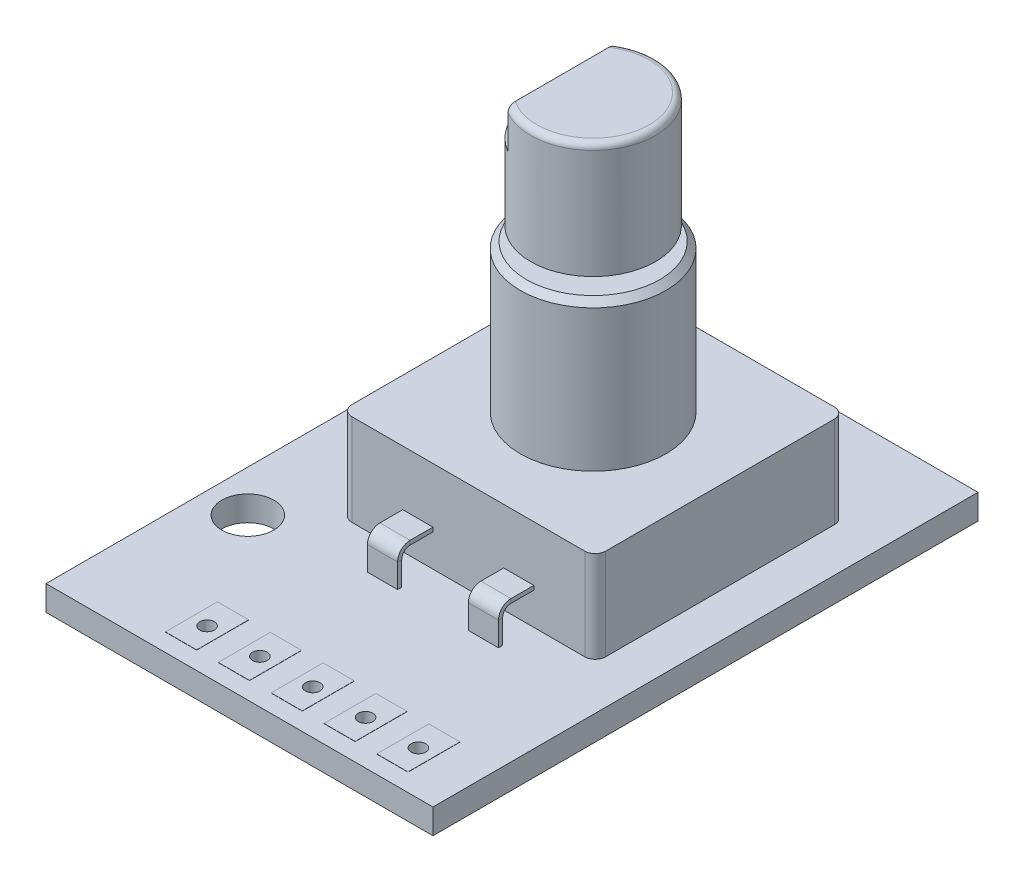
SolidWorks part; units mm, degrees
ref_plane "Front Plane" through (0, 0, 0) normal (0, 0, 1) x (1, 0, 0)
ref_plane "Top Plane" through (0, 0, 0) normal (0, 1, 0) x (1, 0, 0)
ref_plane "Right Plane" through (0, 0, 0) normal (1, 0, 0) x (0, 0, -1)
sketch "Sketch1" plane through (0, 0, 0) normal (0, 1, 0) x (1, 0, 0)
  line L0 (-7.3, 8.3) -> (-7.3, -5.4) construction
  line L1 (-9.3, 13.1) -> (9.3, 13.1)
  line L2 (-9.3, 13.1) -> (-9.3, -13.1)
  line L3 (-9.3, -13.1) -> (9.3, -13.1)
  line L4 (9.3, 13.1) -> (9.3, -13.1)
  line L5 (-9.3, 13.1) -> (9.3, -13.1) construction
  line L6 (-9.3, -13.1) -> (9.3, 13.1) construction
  circle A0 centre (-7.3, 8.3) radius 1.25
  circle A1 centre (-7.3, -5.4) radius 1.25
  point P0 (0, 0)
  dimension "D3" = 2.5
  dimension "D1" = 18.6
  dimension "D2" = 26.2
  dimension "D4" = 13.7
  dimension "D5" = 4.8
  dimension "D6" = 2
extrude "Boss-Extrude1" add sketch "Sketch1" along normal blind 1.2
sketch "Sketch3" plane through (0, 1.2, 0) normal (0, 1, 0) x (1, 0, 0)
  line L0 (9.3, -13.1) -> (9.3, 13.1) construction
  line L1 (-5, -3.2) -> (7.2, -3.2)
  line L2 (-5, -3.2) -> (-5, 8.8)
  line L3 (-5, 8.8) -> (7.2, 8.8)
  line L4 (7.2, -3.2) -> (7.2, 8.8)
  line L5 (-5, -3.2) -> (7.2, 8.8) construction
  line L6 (-5, 8.8) -> (7.2, -3.2) construction
  line L7 (9.3, 13.1) -> (-9.3, 13.1) construction
  point P0 (1.1, 2.8)
  dimension "D1" = 12
  dimension "D2" = 12.2
  dimension "D3" = 2.1
  dimension "D4" = 4.3
extrude "Boss-Extrude2" add sketch "Sketch3" along normal blind 4.4
sketch3d "3DSketch5"
  line L0 (1.1, 5.6, 3.2) -> (1.1, 1.2, 3.2) construction
  line L7 (-5, 5.6, 3.2) -> (7.2, 5.6, 3.2) construction
  line L8 (-5, 1.2, 3.2) -> (7.2, 1.2, 3.2) construction
  line L9 (-1.325, 2.85, 3.2) -> (-1.325, 2.85, 4.3)
  line L10 (-1.325, 2.35, 4.8) -> (-1.325, 1.2, 4.8)
  arc A0 (-1.325, 2.85, 4.3) -> (-1.325, 2.35, 4.8) centre (-1.325, 2.35, 4.3) ccw
  point P0 (-1.325, 2.85, 3.2)
  point P15 (-1.325, 2.85, 4.8)
  point P16 (-0.825, 2.35, 4.3)
  dimension "D3" = 0.5
  dimension "D1" = 2.425
  dimension "D2" = 1.65
  dimension "D5" = 1.6
sketch "Sketch10" plane through (0, 0, 3.2) normal (0, 0, 1) x (1, 0, 0)
  line L1 (-2.05, 2.75) -> (-0.6, 2.75)
  line L2 (-2.05, 2.75) -> (-2.05, 2.95)
  line L3 (-2.05, 2.95) -> (-0.6, 2.95)
  line L4 (-0.6, 2.75) -> (-0.6, 2.95)
  line L5 (-2.05, 2.75) -> (-0.6, 2.95) construction
  line L6 (-2.05, 2.95) -> (-0.6, 2.75) construction
  point P0 (-1.325, 2.85)
  dimension "D1" = 1.45
  dimension "D2" = 0.2
sweep "Sweep3" add profiles "Sketch10" path "3DSketch5"
ref_plane "Plane4" through (1.1, 0, 0) normal (-1, 0, 0) x (0, 0, 1)
mirror "Mirror2" about plane through (1.1, 0, 0) normal (-1, 0, 0) of "Sweep3"
sketch "Sketch13" plane through (0, 0, -8.8) normal (0, 0, -1) x (-1, 0, 0)
  line L0 (-1.1, 5.6) -> (-1.1, 1.2) construction
  line L1 (-1.825, 2.7) -> (-0.375, 2.7)
  line L2 (-1.825, 2.7) -> (-1.825, 2.9)
  line L3 (-1.825, 2.9) -> (-0.375, 2.9)
  line L4 (-0.375, 2.7) -> (-0.375, 2.9)
  line L5 (-1.825, 2.7) -> (-0.375, 2.9) construction
  line L6 (-1.825, 2.9) -> (-0.375, 2.7) construction
  line L7 (-7.2, 5.6) -> (5, 5.6) construction
  line L8 (-7.2, 1.2) -> (5, 1.2) construction
  point P0 (-1.1, 2.8)
  dimension "D1" = 1.45
  dimension "D2" = 0.2
  dimension "D5" = 1.6
sketch3d "3DSketch6"
  line L2 (1.1, 2.8, -8.8) -> (1.1, 2.8, -9.75)
  line L6 (1.1, 2.3, -10.25) -> (1.1, 1.2, -10.25)
  arc A0 (1.1, 2.8, -9.75) -> (1.1, 2.3, -10.25) centre (1.1, 2.3, -9.75) ccw
  point P2 (1.1, 2.8, -10.25)
  point P5 (0.6, 2.3, -9.75)
  dimension "D2" = 0.5
  dimension "D1" = 1.45
sweep "Sweep4" add profiles "Sketch13" path "3DSketch6"
pattern_linear "LPattern1" count 2 spacing 2.85 along (-1, 0, 0) of "Sweep4"
pattern_linear "LPattern2" count 2 spacing 2.85 along (1, 0, 0) of "Sweep4"
sketch "Sketch14" plane through (0, 5.6, 0) normal (0, 1, 0) x (1, 0, 0)
  line L0 (-5, 8.8) -> (7.2, -3.2) construction
  line L1 (-5, -3.2) -> (7.2, 8.8) construction
  circle A0 centre (1.1, 2.8) radius 3.5
  dimension "D1" = 7
extrude "Boss-Extrude4" add sketch "Sketch14" along normal blind 7.1
chamfer "Chamfer1" distance 0.3 angle 45 1 edges at (1.1, 12.7, 0.7)
sketch "Sketch15" plane through (0, 12.7, 0) normal (0, 1, 0) x (1, 0, 0)
  circle A2 centre (1.1, 2.8) radius 1.9
  circle A3 centre (1.1, 2.8) radius 1.9
  dimension "D1" = 1.3
extrude "Boss-Extrude5" add sketch "Sketch15" along normal blind 0.65
sketch "Sketch16" plane through (0, 13.35, 0) normal (0, 1, 0) x (1, 0, 0)
  circle A0 centre (1.1, 2.8) radius 3
  dimension "D1" = 6
extrude "Boss-Extrude6" add sketch "Sketch16" along normal blind 14.45
chamfer "Chamfer2" distance 0.6 angle 45 1 edges at (1.1, 27.8, 0.2)
sketch "Sketch17" plane through (0, 27.8, 0) normal (0, 1, 0) x (1, 0, 0)
  line L0 (-0.3967, 5.4) -> (-0.3967, 0.2)
  circle A1 centre (1.1, 2.8) radius 3
  arc A2 (-0.3967, 5.4) -> (-0.3967, 0.2) centre (1.1, 2.8) ccw
  dimension "D2" = 5.2
  dimension "D1" = 0
extrude "Cut-Extrude1" cut sketch "Sketch17" against normal blind 10.8
sketch "Sketch18" plane through (0, 1.2, 0) normal (0, 1, 0) x (1, 0, 0)
  line L0 (-9.3, -13.1) -> (9.3, -13.1) construction
  line L1 (9.3, -13.1) -> (9.3, 13.1) construction
  circle A0 centre (6.5, -11) radius 0.35
  circle A1 centre (3.96, -11) radius 0.35
  circle A2 centre (1.42, -11) radius 0.35
  circle A3 centre (-1.12, -11) radius 0.35
  circle A4 centre (-3.66, -11) radius 0.35
  dimension "D1" = 0.7
  dimension "D2" = 2.1
  dimension "D3" = 2.8
  dimension "D4" = 5
extrude "Cut-Extrude2" cut sketch "Sketch18" against normal up to surface (1.2 mm away) up to face at (0, 0, 0)
sketch "Sketch19" plane through (0, 1.2, 0) normal (0, 1, 0) x (1, 0, 0)
  line L0 (4.71, -12.25) -> (4.71, -9.75)
  line L1 (5.75, -12.25) -> (7.25, -12.25)
  line L2 (5.75, -12.25) -> (5.75, -9.75)
  line L3 (5.75, -9.75) -> (7.25, -9.75)
  line L4 (7.25, -12.25) -> (7.25, -9.75)
  line L5 (5.75, -12.25) -> (7.25, -9.75) construction
  line L6 (5.75, -9.75) -> (7.25, -12.25) construction
  line L7 (3.21, -9.75) -> (4.71, -9.75)
  line L8 (3.21, -12.25) -> (3.21, -9.75)
  line L9 (3.21, -12.25) -> (4.71, -12.25)
  line L10 (2.17, -12.25) -> (2.17, -9.75)
  line L11 (0.67, -9.75) -> (2.17, -9.75)
  line L12 (0.67, -12.25) -> (0.67, -9.75)
  line L13 (0.67, -12.25) -> (2.17, -12.25)
  line L14 (-0.37, -12.25) -> (-0.37, -9.75)
  line L15 (-1.87, -9.75) -> (-0.37, -9.75)
  line L16 (-1.87, -12.25) -> (-1.87, -9.75)
  line L17 (-1.87, -12.25) -> (-0.37, -12.25)
  line L18 (-2.91, -12.25) -> (-2.91, -9.75)
  line L19 (-4.41, -9.75) -> (-2.91, -9.75)
  line L20 (-4.41, -12.25) -> (-4.41, -9.75)
  line L21 (-4.41, -12.25) -> (-2.91, -12.25)
  circle A0 centre (6.5, -11) radius 0.35
  circle A1 centre (3.96, -11) radius 0.35
  circle A2 centre (1.42, -11) radius 0.35
  circle A3 centre (-1.12, -11) radius 0.35
  circle A4 centre (-3.66, -11) radius 0.35
  point P0 (6.5, -11)
  dimension "D3" = 5
  dimension "D1" = 2.5
  dimension "D2" = 1.5
extrude "Boss-Extrude7" add sketch "Sketch19" along normal blind 0.01
ref_plane "Plane5" through (0, 0.6, 0) normal (0, 1, 0) x (1, 0, 0)
mirror "Mirror3" about plane through (0, 0.6, 0) normal (0, 1, 0) of "Boss-Extrude7"
fillet "Fillet1" radius 0.5 4 edges at (-5, 3.4, -8.8) (-5, 3.4, 3.2) (7.2, 3.4, 3.2) (7.2, 3.4, -8.8)
sketch "Croquis1" plane through (0, 27.8, 0) normal (0, 1, 0) x (1, 0, 0)
  circle A0 centre (1.1, 2.8) radius 3.5
extrude "Cortar-Extruir1" cut sketch "Croquis1" against normal blind 8.9
fillet "Redondeo1" radius 0.3 1 edges at (4.1, 18.9, -2.8)
